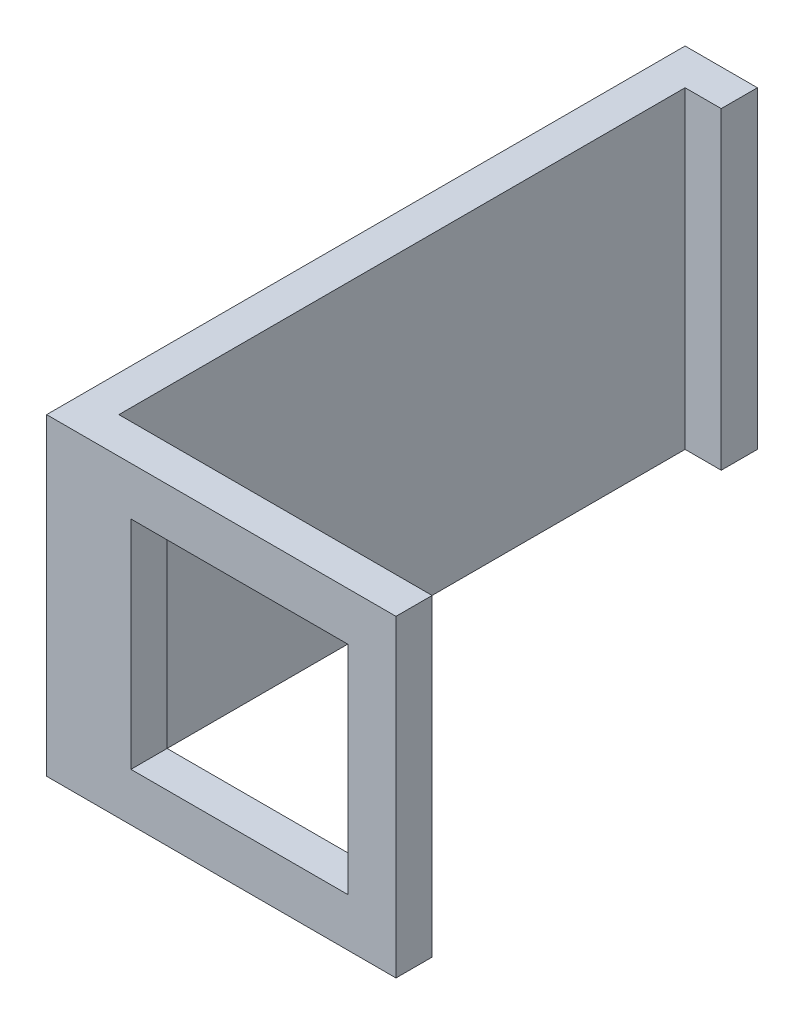
SolidWorks part; units mm, degrees
ref_plane "Front Plane" through (0, 0, 0) normal (0, 0, 1) x (1, 0, 0)
ref_plane "Top Plane" through (0, 0, 0) normal (0, 1, 0) x (1, 0, 0)
ref_plane "Right Plane" through (0, 0, 0) normal (1, 0, 0) x (0, 0, -1)
sketch "Sketch1" plane through (0, 0, 0) normal (0, 0, 1) x (1, 0, 0)
  line L0 (5.25, 4.5) -> (-3.75, 4.5)
  line L1 (7.25, -6.5) -> (-7.25, -6.5)
  line L2 (7.25, -6.5) -> (7.25, 6.5)
  line L3 (7.25, 6.5) -> (-7.25, 6.5)
  line L4 (-7.25, -6.5) -> (-7.25, 6.5)
  line L5 (7.25, -6.5) -> (-7.25, 6.5) construction
  line L6 (7.25, 6.5) -> (-7.25, -6.5) construction
  line L7 (-3.75, -4.5) -> (-3.75, 4.5)
  line L8 (5.25, -4.5) -> (-3.75, -4.5)
  line L9 (5.25, -4.5) -> (5.25, 4.5)
  line L10 (-3.75, 4.5) -> (5.25, -4.5) construction
  line L11 (-3.75, -4.5) -> (5.25, 4.5) construction
  point P0 (0, 0)
  dimension "D1" = 14.5
  dimension "D3" = 13
  dimension "D2" = 2
  dimension "D4" = 2
  dimension "D5" = 2
  dimension "D6" = 9
extrude "Boss-Extrude1" add sketch "Sketch1" along normal blind 1.5
sketch "Sketch2" plane through (0, 0, 0) normal (0, 0, -1) x (-1, 0, 0)
  line L1 (5.75, 6.5) -> (7.25, 6.5)
  line L2 (5.75, 6.5) -> (5.75, -6.5)
  line L3 (5.75, -6.5) -> (7.25, -6.5)
  line L4 (7.25, 6.5) -> (7.25, -6.5)
  line L5 (5.75, 6.5) -> (7.25, -6.5) construction
  line L6 (5.75, -6.5) -> (7.25, 6.5) construction
  point P0 (6.5, 0)
  dimension "D1" = 1.5
extrude "Boss-Extrude2" add sketch "Sketch2" along normal blind 25
sketch "Sketch3" plane through (-5.75, 0, 0) normal (1, 0, 0) x (0, 0, -1)
  line L1 (23.5, -6.5) -> (25, -6.5)
  line L2 (23.5, -6.5) -> (23.5, 6.5)
  line L3 (23.5, 6.5) -> (25, 6.5)
  line L4 (25, -6.5) -> (25, 6.5)
  line L5 (23.5, -6.5) -> (25, 6.5) construction
  line L6 (23.5, 6.5) -> (25, -6.5) construction
  point P0 (24.25, 0)
  dimension "D1" = 1.5
extrude "Boss-Extrude3" add sketch "Sketch3" along normal blind 1.5
